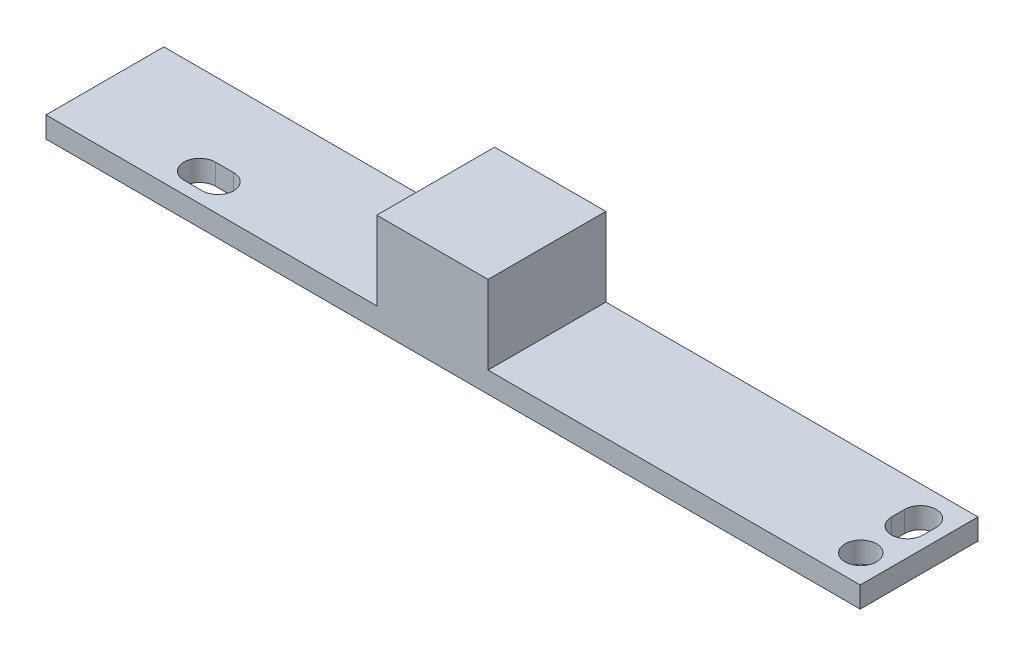
SolidWorks part; units mm, degrees
ref_plane "Front Plane" through (0, 0, 0) normal (0, 0, 1) x (1, 0, 0)
ref_plane "Top Plane" through (0, 0, 0) normal (0, 1, 0) x (1, 0, 0)
ref_plane "Right Plane" through (0, 0, 0) normal (1, 0, 0) x (0, 0, -1)
sketch "Sketch1" plane through (0, 0, 0) normal (0, 1, 0) x (1, 0, 0)
  line L1 (0, 0) -> (62.2, 0)
  line L2 (0, 0) -> (0, 9)
  line L3 (0, 9) -> (62.2, 9)
  line L4 (62.2, 0) -> (62.2, 9)
  dimension "D1" = 62.2
  dimension "D2" = 9
extrude "Boss-Extrude1" add sketch "Sketch1" along normal blind 1.6
sketch "Sketch2" plane through (0, 1.6, 0) normal (0, 1, 0) x (1, 0, 0)
  line L0 (9.5916, 2.1472) -> (10.9916, 2.1472) construction
  line L1 (9.5916, 3.3472) -> (10.9916, 3.3472)
  line L2 (9.5916, 0.9472) -> (10.9916, 0.9472)
  line L3 (60.0982, 6.7) -> (60.0982, 5.7) construction
  line L4 (61.2982, 6.7) -> (61.2982, 5.7)
  line L5 (58.8982, 6.7) -> (58.8982, 5.7)
  line L6 (60.0982, 7.9) -> (60.0982, 6.7) construction
  line L7 (60.0982, 5.7) -> (60.0982, 4.5) construction
  line L8 (60.0982, 4.5) -> (60.0982, 2.1472) construction
  line L9 (62.2, 4.5) -> (0, 4.5) construction
  line L10 (62.2, 0) -> (62.2, 9) construction
  line L11 (0, 9) -> (0, 0) construction
  line L12 (9.5916, 2.1472) -> (8.3916, 2.1472) construction
  line L13 (8.3916, 2.1472) -> (10.2916, 3.3472) construction
  line L14 (10.2916, 3.3472) -> (12.1916, 2.1472) construction
  line L15 (12.1916, 2.1472) -> (10.9916, 2.1472) construction
  line L16 (12.1916, 2.1472) -> (60.0982, 2.1472) construction
  line L17 (61.2982, 2.1472) -> (62.2, 2.1472) construction
  arc A0 (9.5916, 3.3472) -> (9.5916, 0.9472) centre (9.5916, 2.1472) ccw
  arc A1 (10.9916, 0.9472) -> (10.9916, 3.3472) centre (10.9916, 2.1472) ccw
  arc A2 (61.2982, 6.7) -> (58.8982, 6.7) centre (60.0982, 6.7) ccw
  arc A3 (58.8982, 5.7) -> (61.2982, 5.7) centre (60.0982, 5.7) ccw
  circle A4 centre (60.0982, 2.1472) radius 1.2
  point P2 (10.2916, 2.1472)
  point P7 (60.0982, 6.2)
  dimension "D1" = 2.4
  dimension "D2" = 3.4
  dimension "D3" = 3.8
extrude "Cut-Extrude1" cut sketch "Sketch2" against normal through all
sketch "Sketch3" plane through (0, 1.6, 0) normal (0, 1, 0) x (1, 0, 0)
  line L0 (0, 4.5) -> (62.2, 4.5) construction
  line L1 (0, 9) -> (0, 0) construction
  line L2 (62.2, 0) -> (62.2, 9) construction
  line L3 (62.2, 9) -> (0, 9) construction
  line L4 (25.27, 0) -> (33.77, 0)
  line L5 (25.27, 0) -> (25.27, 9)
  line L6 (25.27, 9) -> (33.77, 9)
  line L7 (33.77, 0) -> (33.77, 9)
  line L8 (25.27, 0) -> (33.77, 9) construction
  line L9 (25.27, 9) -> (33.77, 0) construction
  point P6 (29.52, 4.5)
  dimension "D1" = 8.5
  dimension "D2" = 28.43
extrude "Boss-Extrude2" add sketch "Sketch3" along normal blind 6
ref_plane "Plane1" through (29.52, 0, 0) normal (1, 0, 0) x (0, 0, -1)
